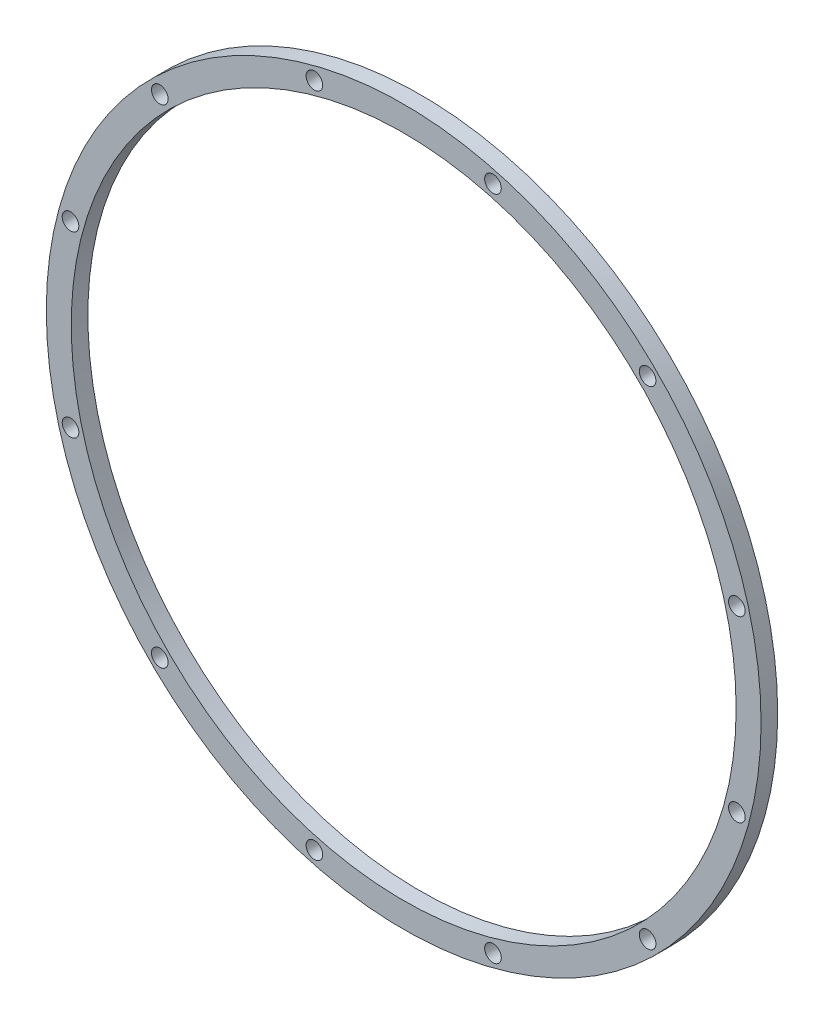
SolidWorks part; units mm, degrees
ref_plane "Front Plane" through (0, 0, 0) normal (0, 0, 1) x (1, 0, 0)
ref_plane "Top Plane" through (0, 0, 0) normal (0, 1, 0) x (1, 0, 0)
ref_plane "Right Plane" through (0, 0, 0) normal (1, 0, 0) x (0, 0, -1)
sketch "FlangeSketch" plane through (0, 0, 0) normal (0, 0, 1) x (1, 0, 0)
  circle A0 centre (0, 0) radius 546.1011
  circle A1 centre (0, 0) radius 508.001
  circle A2 centre (0, 0) radius 508.001 construction
  dimension "FlangeWidth" = 38.1001
extrude "FlangeFeature" add sketch "FlangeSketch" along normal blind 25.4001
sketch "Sketch2" plane through (0, 0, 25.4001) normal (0, 0, 1) x (1, 0, 0)
  line L0 (0, 0) -> (0, 527.0511) construction
  line L1 (0, 0) -> (-136.4109, 509.0923) construction
  circle A0 centre (0, 0) radius 527.0511 construction
  circle A1 centre (0, 0) radius 546.1011 construction
  circle A2 centre (-136.4109, 509.0923) radius 12.7
  dimension "D1" = 19.05
  dimension "BoltDiameter" = 25.4
  dimension "D2" = 15
extrude "Bolt Hole" cut sketch "Sketch2" against normal through all contours A2
pattern_circular "BoltPattern" count 12 over 360 about axis through (0, 0, 0) along (0, 0, 1) of "Bolt Hole"
equation "\"BoltHoleQty\"= 12"
equation "\"AngleStart\"= 180 / \"BoltHoleQty\""
equation "\"D1@BoltPattern\" = \"BoltHoleQty\""
